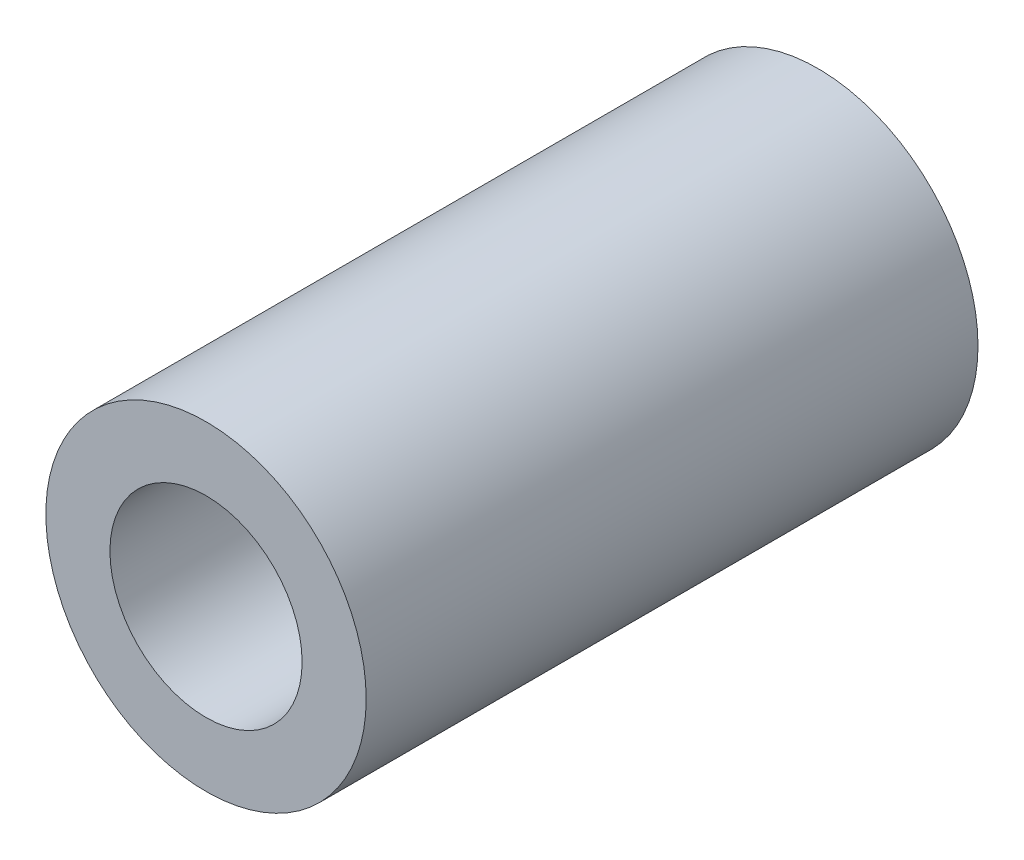
SolidWorks part; units mm, degrees
material "ﾎﾟﾘｵｷｼﾒﾁﾚﾝ(POM)ｱｾﾀｰﾙ共重合体"
ref_plane "Front Plane" through (0, 0, 0) normal (0, 0, 1) x (1, 0, 0)
ref_plane "Top Plane" through (0, 0, 0) normal (0, 1, 0) x (1, 0, 0)
ref_plane "Right Plane" through (0, 0, 0) normal (1, 0, 0) x (0, 0, -1)
sketch "Sketch2" plane through (0, 0, 0) normal (0, 0, 1) x (1, 0, 0)
  circle A0 centre (0, 0) radius 2.5
  circle A1 centre (0, 0) radius 1.5
  dimension "D1" = 3
  dimension "D2" = 5
  dimension "D3" = 5
extrude "Boss-Extrude1" add sketch "Sketch2" along normal blind 9.55
